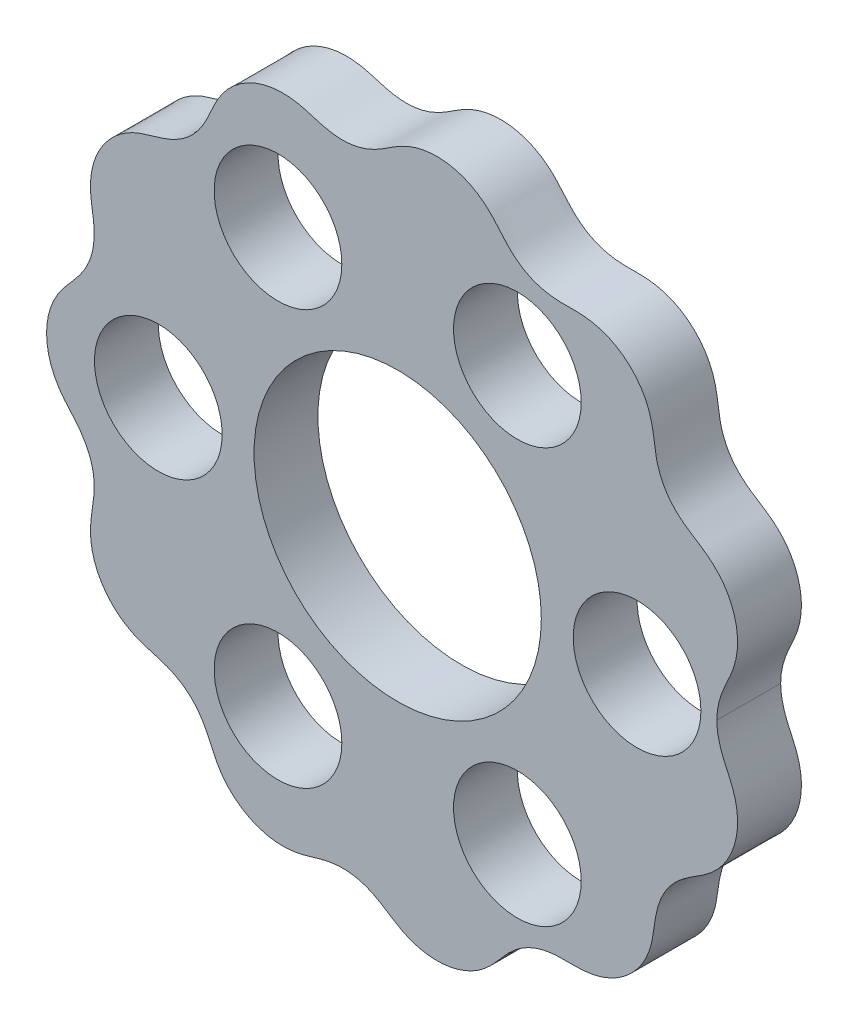
SolidWorks part; units mm, degrees
material "6061-T6 (SS)"
ref_plane "Front Plane" through (0, 0, 0) normal (0, 0, 1) x (1, 0, 0)
ref_plane "Top Plane" through (0, 0, 0) normal (0, 1, 0) x (1, 0, 0)
ref_plane "Right Plane" through (0, 0, 0) normal (1, 0, 0) x (0, 0, -1)
sketch "Sketch3" plane through (0, 0, 0) normal (0, 0, 1) x (1, 0, 0)
  line L0 (-1000, 0) -> (49000, 0) construction
  spline S0 degree 4 poles (33.5396, 9.7368) (33.6384, 9.3818) (33.7859, 8.6752) (33.8555, 7.776) (33.7639, 6.704) (33.5817, 5.8571) (33.3816, 5.2122) (33.1388, 4.598) (32.8711, 4.0107) (32.6156, 3.4698) (32.3925, 2.9656) (32.2292, 2.5493) (32.1171, 2.2253) (32.0335, 1.9521) (31.973, 1.7317) (31.9119, 1.4793) (31.8541, 1.1955) (31.8108, 0.9204) (31.7809, 0.6592) (31.7635, 0.4431) (31.7543, 0.2567) (31.7496, 0.0625) (31.7496, -0.0657) (31.7538, -0.2388) (31.7605, -0.3825) (31.7696, -0.5196) (31.7811, -0.6523) (31.798, -0.8077) (31.822, -0.9867) (31.8507, -1.1647) (31.8978, -1.4156) (31.9716, -1.7383) (32.0825, -2.1294) (32.2407, -2.5845) (32.4357, -3.0671) (32.6656, -3.5769) (32.9213, -4.1173) (33.1813, -4.6987) (33.4812, -5.4811) (33.7479, -6.4878) (33.8713, -7.7288) (33.7333, -9.1646) (33.3265, -10.5417) (32.6698, -11.8117) (31.818, -12.8884) (30.8236, -13.758) (29.8039, -14.4116) (28.8631, -14.9919) (27.9385, -15.6906) (27.0867, -16.553) (26.4316, -17.5358) (25.9847, -18.5854) (25.6953, -19.6621) (25.5292, -20.7393) (25.3921, -21.9604) (25.0559, -23.294) (24.4668, -24.5642) (23.6323, -25.7176) (22.5958, -26.6926) (21.3941, -27.4565) (19.915, -28.0383) (18.3968, -28.2721) (16.9369, -28.2142) (15.4768, -28.2426) (14.1936, -28.4587) (12.8979, -28.9484) (11.688, -29.7428) (10.6627, -30.7568) (9.8709, -31.7499) (9.1294, -32.5455) (8.2984, -33.2464) (7.3823, -33.8359) (6.2278, -34.335) (4.8383, -34.6437) (3.4157, -34.6857) (2.1386, -34.4791) (1.0411, -34.1018) (0.0298, -33.5899) (-0.8958, -32.9849) (-1.9242, -32.2996) (-3.162, -31.708) (-4.5194, -31.3619) (-5.9194, -31.3158) (-7.2731, -31.5382) (-8.4523, -31.9075) (-9.5114, -32.2258) (-10.6265, -32.4293) (-11.7859, -32.479) (-13.0691, -32.314) (-14.421, -31.8693) (-15.6654, -31.1783) (-16.6304, -30.3715) (-17.341, -29.5458) (-17.9385, -28.6377) (-18.4238, -27.6645) (-18.8977, -26.5041) (-19.5888, -25.2575) (-20.51, -24.1644) (-21.8183, -23.1621) (-23.5023, -22.439) (-25.2865, -22.0876) (-26.9545, -21.3265) (-28.2285, -20.3487) (-29.1734, -19.2834) (-29.9006, -18.0602) (-30.3849, -16.7215) (-30.6021, -15.3298) (-30.5548, -13.9383) (-30.3383, -12.7118) (-30.1922, -11.6149) (-30.1694, -10.4918) (-30.3055, -9.3591) (-30.6609, -8.2329) (-31.2379, -7.1667) (-31.84, -6.3601) (-32.3655, -5.7539) (-32.833, -5.2269) (-33.223, -4.762) (-33.6016, -4.2555) (-33.9541, -3.7002) (-34.227, -3.1718) (-34.4323, -2.6821) (-34.5769, -2.264) (-34.6764, -1.9246) (-34.7595, -1.5803) (-34.8262, -1.2335) (-34.87, -0.9258) (-34.8971, -0.6626) (-34.9128, -0.4454) (-34.9212, -0.2583) (-34.9253, -0.0639) (-34.9253, 0.0636) (-34.9212, 0.2576) (-34.9129, 0.4445) (-34.8973, 0.6613) (-34.8702, 0.9238) (-34.8266, 1.2309) (-34.7602, 1.5769) (-34.6775, 1.9206) (-34.5784, 2.2592) (-34.4632, 2.5931) (-34.3322, 2.9209) (-34.1857, 3.2422) (-34.024, 3.5561) (-33.8175, 3.9152) (-33.5575, 4.3131) (-33.1482, 4.8642) (-32.5887, 5.5067) (-31.9479, 6.2172) (-31.351, 7.0124) (-30.9082, 7.7733) (-30.6605, 8.3474) (-30.5393, 8.6968) (-30.4853, 8.8736) knots 0 0 0 0 0 0.011116 0.021732 0.027039 0.032346 0.037213 0.042081 0.046948 0.051816 0.055263 0.058711 0.060434 0.062158 0.063882 0.065605 0.06826 0.070914 0.072241 0.073568 0.074896 0.076223 0.077581 0.078939 0.079618 0.080297 0.081655 0.083013 0.084371 0.085729 0.087087 0.090719 0.094352 0.097984 0.101617 0.106419 0.111221 0.116023 0.120824 0.131683 0.142543 0.153402 0.164074 0.174746 0.185416 0.194568 0.203719 0.211245 0.218771 0.229448 0.240126 0.246585 0.253045 0.263011 0.272978 0.28365 0.294321 0.304993 0.315665 0.326337 0.337009 0.352677 0.36152 0.370362 0.381038 0.391712 0.403004 0.413672 0.424341 0.430042 0.435742 0.446413 0.457086 0.467757 0.47843 0.489101 0.495868 0.502636 0.512543 0.522451 0.533129 0.543807 0.554485 0.564392 0.5743 0.581067 0.587834 0.598505 0.609178 0.61985 0.630522 0.641193 0.646894 0.652594 0.663263 0.673932 0.684719 0.695397 0.706071 0.723257 0.739426 0.750098 0.760769 0.771441 0.782113 0.792786 0.803456 0.813673 0.823891 0.83035 0.836809 0.847488 0.858164 0.86569 0.873216 0.877792 0.882368 0.886943 0.891519 0.896854 0.90219 0.904858 0.907526 0.910194 0.912862 0.91553 0.918198 0.919532 0.920866 0.9222 0.923534 0.924865 0.926196 0.927527 0.928858 0.931521 0.934183 0.936845 0.939507 0.942169 0.944831 0.947493 0.950155 0.952818 0.95548 0.959986 0.964492 0.973504 0.981176 0.988848 0.994424 1 1 1 1 1 construction
  spline S1 degree 4 poles (31.75, 0) (31.75, -0.0381) (31.7508, -0.1144) (31.7538, -0.2388) (31.7605, -0.3825) (31.7696, -0.5196) (31.7811, -0.6523) (31.798, -0.8077) (31.822, -0.9867) (31.8507, -1.1647) (31.8978, -1.4156) (31.9716, -1.7383) (32.0825, -2.1294) (32.2407, -2.5845) (32.4357, -3.0671) (32.6656, -3.5769) (32.9213, -4.1173) (33.1813, -4.6987) (33.4812, -5.4811) (33.7479, -6.4878) (33.8713, -7.7288) (33.7333, -9.1646) (33.3265, -10.5417) (32.6698, -11.8117) (31.818, -12.8884) (30.8236, -13.758) (29.8039, -14.4116) (28.8631, -14.9919) (27.9385, -15.6906) (27.0867, -16.553) (26.4316, -17.5358) (25.9847, -18.5854) (25.6953, -19.6621) (25.5292, -20.7393) (25.3921, -21.9604) (25.0559, -23.294) (24.4668, -24.5642) (23.6323, -25.7176) (22.5958, -26.6926) (21.3941, -27.4565) (19.915, -28.0383) (18.3968, -28.2721) (16.9369, -28.2142) (15.4768, -28.2426) (14.1936, -28.4587) (12.8979, -28.9484) (11.688, -29.7428) (10.6627, -30.7568) (9.8709, -31.7499) (9.1294, -32.5455) (8.2984, -33.2464) (7.3823, -33.8359) (6.2278, -34.335) (4.8383, -34.6437) (3.4157, -34.6857) (2.1386, -34.4791) (1.0411, -34.1018) (0.0298, -33.5899) (-0.8958, -32.9849) (-1.9242, -32.2996) (-3.162, -31.708) (-4.5194, -31.3619) (-5.9194, -31.3158) (-7.2731, -31.5382) (-8.4523, -31.9075) (-9.5114, -32.2258) (-10.6265, -32.4293) (-11.7859, -32.479) (-13.0691, -32.314) (-14.421, -31.8693) (-15.6654, -31.1783) (-16.6304, -30.3715) (-17.341, -29.5458) (-17.9385, -28.6377) (-18.4238, -27.6645) (-18.8977, -26.5041) (-19.5888, -25.2575) (-20.51, -24.1644) (-21.8183, -23.1621) (-23.5023, -22.439) (-25.2865, -22.0876) (-26.9545, -21.3265) (-28.2285, -20.3487) (-29.1734, -19.2834) (-29.9006, -18.0602) (-30.3849, -16.7215) (-30.6021, -15.3298) (-30.5548, -13.9383) (-30.3383, -12.7118) (-30.1922, -11.6149) (-30.1694, -10.4918) (-30.3055, -9.3591) (-30.6609, -8.2329) (-31.2379, -7.1667) (-31.84, -6.3601) (-32.3655, -5.7539) (-32.833, -5.2269) (-33.223, -4.762) (-33.6016, -4.2555) (-33.9541, -3.7002) (-34.227, -3.1718) (-34.4323, -2.6821) (-34.5769, -2.264) (-34.6764, -1.9246) (-34.7595, -1.5803) (-34.8262, -1.2335) (-34.87, -0.9258) (-34.8971, -0.6626) (-34.9128, -0.4454) (-34.9212, -0.2583) (-34.9243, -0.1124) (-34.925, -0.0375) (-34.925, 0) knots 0.076223 0.076223 0.076223 0.076223 0.076223 0.077581 0.078939 0.079618 0.080297 0.081655 0.083013 0.084371 0.085729 0.087087 0.090719 0.094352 0.097984 0.101617 0.106419 0.111221 0.116023 0.120824 0.131683 0.142543 0.153402 0.164074 0.174746 0.185416 0.194568 0.203719 0.211245 0.218771 0.229448 0.240126 0.246585 0.253045 0.263011 0.272978 0.28365 0.294321 0.304993 0.315665 0.326337 0.337009 0.352677 0.36152 0.370362 0.381038 0.391712 0.403004 0.413672 0.424341 0.430042 0.435742 0.446413 0.457086 0.467757 0.47843 0.489101 0.495868 0.502636 0.512543 0.522451 0.533129 0.543807 0.554485 0.564392 0.5743 0.581067 0.587834 0.598505 0.609178 0.61985 0.630522 0.641193 0.646894 0.652594 0.663263 0.673932 0.684719 0.695397 0.706071 0.723257 0.739426 0.750098 0.760769 0.771441 0.782113 0.792786 0.803456 0.813673 0.823891 0.83035 0.836809 0.847488 0.858164 0.86569 0.873216 0.877792 0.882368 0.886943 0.891519 0.896854 0.90219 0.904858 0.907526 0.910194 0.912862 0.91553 0.918198 0.919532 0.920866 0.9222 0.923534 0.923534 0.923534 0.923534 0.923534
  spline S2 degree 4 poles (31.75, 0) (31.75, 0.0381) (31.7508, 0.1144) (31.7538, 0.2388) (31.7605, 0.3825) (31.7696, 0.5196) (31.7811, 0.6523) (31.798, 0.8077) (31.822, 0.9867) (31.8507, 1.1647) (31.8978, 1.4156) (31.9716, 1.7383) (32.0825, 2.1294) (32.2407, 2.5845) (32.4357, 3.0671) (32.6656, 3.5769) (32.9213, 4.1173) (33.1813, 4.6987) (33.4812, 5.4811) (33.7479, 6.4878) (33.8713, 7.7288) (33.7333, 9.1646) (33.3265, 10.5417) (32.6698, 11.8117) (31.818, 12.8884) (30.8236, 13.758) (29.8039, 14.4116) (28.8631, 14.9919) (27.9385, 15.6906) (27.0867, 16.553) (26.4316, 17.5358) (25.9847, 18.5854) (25.6953, 19.6621) (25.5292, 20.7393) (25.3921, 21.9604) (25.0559, 23.294) (24.4668, 24.5642) (23.6323, 25.7176) (22.5958, 26.6926) (21.3941, 27.4565) (19.915, 28.0383) (18.3968, 28.2721) (16.9369, 28.2142) (15.4768, 28.2426) (14.1936, 28.4587) (12.8979, 28.9484) (11.688, 29.7428) (10.6627, 30.7568) (9.8709, 31.7499) (9.1294, 32.5455) (8.2984, 33.2464) (7.3823, 33.8359) (6.2278, 34.335) (4.8383, 34.6437) (3.4157, 34.6857) (2.1386, 34.4791) (1.0411, 34.1018) (0.0298, 33.5899) (-0.8958, 32.9849) (-1.9242, 32.2996) (-3.162, 31.708) (-4.5194, 31.3619) (-5.9194, 31.3158) (-7.2731, 31.5382) (-8.4523, 31.9075) (-9.5114, 32.2258) (-10.6265, 32.4293) (-11.7859, 32.479) (-13.0691, 32.314) (-14.421, 31.8693) (-15.6654, 31.1783) (-16.6304, 30.3715) (-17.341, 29.5458) (-17.9385, 28.6377) (-18.4238, 27.6645) (-18.8977, 26.5041) (-19.5888, 25.2575) (-20.51, 24.1644) (-21.8183, 23.1621) (-23.5023, 22.439) (-25.2865, 22.0876) (-26.9545, 21.3265) (-28.2285, 20.3487) (-29.1734, 19.2834) (-29.9006, 18.0602) (-30.3849, 16.7215) (-30.6021, 15.3298) (-30.5548, 13.9383) (-30.3383, 12.7118) (-30.1922, 11.6149) (-30.1694, 10.4918) (-30.3055, 9.3591) (-30.6609, 8.2329) (-31.2379, 7.1667) (-31.84, 6.3601) (-32.3655, 5.7539) (-32.833, 5.2269) (-33.223, 4.762) (-33.6016, 4.2555) (-33.9541, 3.7002) (-34.227, 3.1718) (-34.4323, 2.6821) (-34.5769, 2.264) (-34.6764, 1.9246) (-34.7595, 1.5803) (-34.8262, 1.2335) (-34.87, 0.9258) (-34.8971, 0.6626) (-34.9128, 0.4455) (-34.9212, 0.2583) (-34.9243, 0.1124) (-34.925, 0.0375) (-34.925, 0) knots 0.076223 0.076223 0.076223 0.076223 0.076223 0.077581 0.078939 0.079618 0.080297 0.081655 0.083013 0.084371 0.085729 0.087087 0.090719 0.094352 0.097984 0.101617 0.106419 0.111221 0.116023 0.120824 0.131683 0.142543 0.153402 0.164074 0.174746 0.185416 0.194568 0.203719 0.211245 0.218771 0.229448 0.240126 0.246585 0.253045 0.263011 0.272978 0.28365 0.294321 0.304993 0.315665 0.326337 0.337009 0.352677 0.36152 0.370362 0.381038 0.391712 0.403004 0.413672 0.424341 0.430042 0.435742 0.446413 0.457086 0.467757 0.47843 0.489101 0.495868 0.502636 0.512543 0.522451 0.533129 0.543807 0.554485 0.564392 0.5743 0.581067 0.587834 0.598505 0.609178 0.61985 0.630522 0.641193 0.646894 0.652594 0.663263 0.673932 0.684719 0.695397 0.706071 0.723257 0.739426 0.750098 0.760769 0.771441 0.782113 0.792786 0.803456 0.813673 0.823891 0.83035 0.836809 0.847488 0.858164 0.86569 0.873216 0.877792 0.882368 0.886943 0.891519 0.896854 0.90219 0.904858 0.907526 0.910194 0.912862 0.91553 0.918198 0.919532 0.920866 0.9222 0.923534 0.923534 0.923534 0.923534 0.923534
extrude "Main Profile" add sketch "Sketch3" along normal blind 6.35
sketch "Sketch4" plane through (0, 0, 6.35) normal (0, 0, 1) x (1, 0, 0)
  line L0 (0, 0) -> (-47.7714, 0) construction
  circle A0 centre (0, 0) radius 14.2875
  circle A1 centre (-23.8125, 0) radius 6.35
  circle A2 centre (0, 0) radius 23.8125 construction
  circle A3 centre (-11.9062, 20.6222) radius 6.35
  circle A4 centre (11.9063, 20.6222) radius 6.35
  circle A5 centre (23.8125, 0) radius 6.35
  circle A6 centre (11.9062, -20.6222) radius 6.35
  circle A7 centre (-11.9063, -20.6222) radius 6.35
  point P26 (0, 0)
  dimension "D1" = 28.575
  dimension "D2" = 12.7
  dimension "D3" = 23.8125
  dimension "D4" = 6
extrude "Cut-Extrude1" cut sketch "Sketch4" against normal through all
equation "\"R\" = 1.5'Rotor Radius"
equation "\"E\"= 0.0625'Eccentricity"
equation "\"Y\"= 0.1875'Roller Radius"
equation "\"N\" = 12'Number of Rollers"
equation "\"O\"= .375'Output Disk Pin Size"
equation "\"D2@Sketch4\"=2 * \"E\"+\"O\""
equation "\"R\"= 10 'Rotor Radius"
